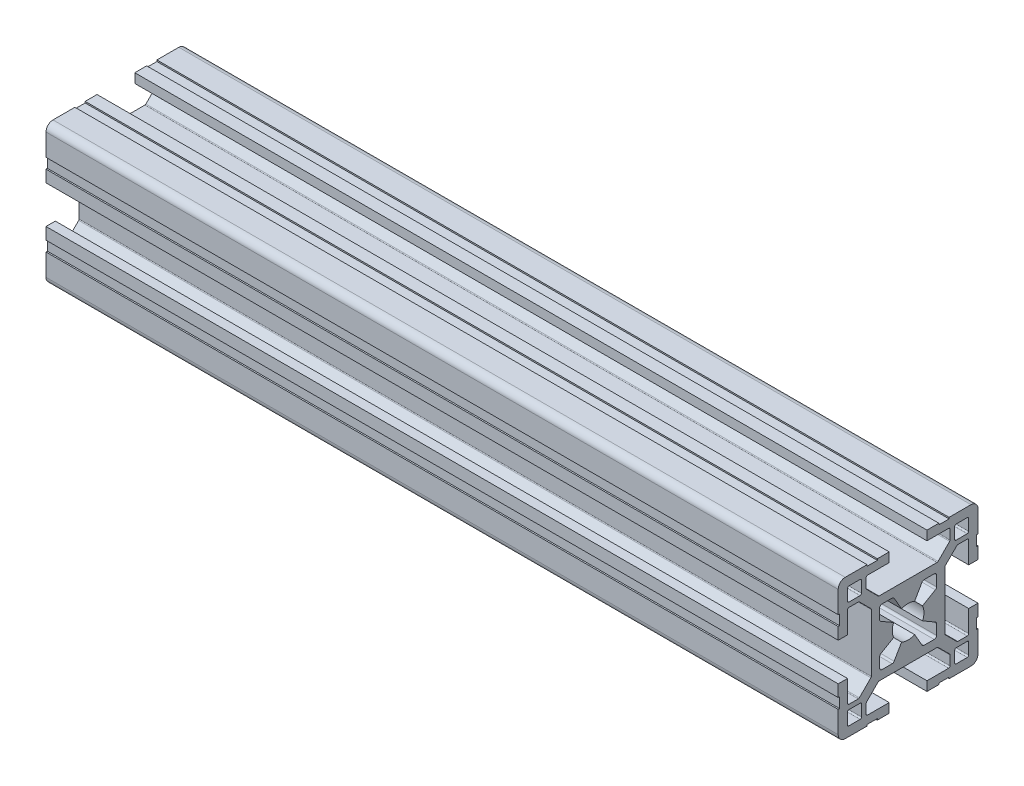
SolidWorks part; units mm, degrees
material "6063-T5"
ref_plane "Plano frontal" through (0, 0, 0) normal (0, 0, 1) x (1, 0, 0)
ref_plane "Plano superior" through (0, 0, 0) normal (0, 1, 0) x (1, 0, 0)
ref_plane "Plano direito" through (0, 0, 0) normal (1, 0, 0) x (0, 0, -1)
sketch "Esboço1" plane through (0, 0, 0) normal (0, 0, 1) x (1, 0, 0)
  line L0 (0, 0) -> (170, 0)
  point P3 (85, 0)
  dimension "D1" = 170
other "Quadrado PF30-11 - PERFIL 3030 CENTRO M8(1)"
ref_plane "Plano1" through (0, 0, 0) normal (1, 0, 0) x (0, 1, 0)
sketch "Sketch1" plane through (0, 0, 0) normal (1, 0, 0) x (0, 1, 0)
  line L0 (-6.1, -3.4254) -> (-6.1, -5.6)
  line L1 (-5.6, -6.1) -> (-3.4254, -6.1)
  line L2 (3.4254, -6.1) -> (5.6, -6.1)
  line L3 (6.1, -5.6) -> (6.1, -3.4254)
  line L4 (6.1, 3.4254) -> (6.1, 5.6)
  line L5 (5.6, 6.1) -> (3.4254, 6.1)
  line L6 (-3.4254, 6.1) -> (-5.6, 6.1)
  line L7 (-6.1, 5.6) -> (-6.1, 3.4254)
  line L8 (15, 6.6) -> (14.7, 6.6)
  line L9 (5.85, -2.9924) -> (3.097, -1.403)
  line L10 (10, 12.7) -> (10, 10.3)
  line L11 (13, -12.7) -> (13, -10.3)
  line L12 (-10.3, -10) -> (-12.7, -10)
  line L13 (-13, 12.7) -> (-13, 10.3)
  line L14 (3.097, 1.403) -> (5.85, 2.9924)
  line L15 (2.9924, 5.85) -> (1.403, 3.097)
  line L16 (-1.403, 3.097) -> (-2.9924, 5.85)
  line L17 (-5.85, 2.9924) -> (-3.097, 1.403)
  line L18 (-3.097, -1.403) -> (-5.85, -2.9924)
  line L19 (-2.9924, -5.85) -> (-1.403, -3.097)
  line L20 (1.403, -3.097) -> (2.9924, -5.85)
  line L21 (10.3, 10) -> (12.7, 10)
  line L22 (13, 10.3) -> (13, 12.7)
  line L23 (12.7, 13) -> (10.3, 13)
  line L24 (12.7, -10) -> (10.3, -10)
  line L25 (10, -10.3) -> (10, -12.7)
  line L26 (10.3, -13) -> (12.7, -13)
  line L27 (-13, -10.3) -> (-13, -12.7)
  line L28 (-12.7, -13) -> (-10.3, -13)
  line L29 (-10, -12.7) -> (-10, -10.3)
  line L30 (-12.7, 10) -> (-10.3, 10)
  line L31 (-10, 10.3) -> (-10, 12.7)
  line L32 (-10.3, 13) -> (-12.7, 13)
  line L33 (15, 4.05) -> (15, 6.6)
  line L34 (13, 4.05) -> (15, 4.05)
  line L35 (13, 8.7) -> (13, 4.05)
  line L36 (10.6799, 9) -> (12.7, 9)
  line L37 (7.9879, 6.4322) -> (10.4678, 8.9121)
  line L38 (7.9, -6.2201) -> (7.9, 6.2201)
  line L39 (10.4678, -8.9121) -> (7.9879, -6.4322)
  line L40 (12.7, -9) -> (10.6799, -9)
  line L41 (13, -4.05) -> (13, -8.7)
  line L42 (15, -4.05) -> (13, -4.05)
  line L43 (15, -6.6) -> (15, -4.05)
  line L44 (14.7, -6.6) -> (15, -6.6)
  line L45 (14.7, -8.8) -> (14.7, -6.6)
  line L46 (15, -8.8) -> (14.7, -8.8)
  line L47 (15, -13.5) -> (15, -8.8)
  line L48 (8.8, -15) -> (13.5, -15)
  line L49 (8.8, -14.7) -> (8.8, -15)
  line L50 (6.6, -14.7) -> (8.8, -14.7)
  line L51 (6.6, -15) -> (6.6, -14.7)
  line L52 (4.05, -15) -> (6.6, -15)
  line L53 (4.05, -13) -> (4.05, -15)
  line L54 (8.7, -13) -> (4.05, -13)
  line L55 (9, -10.6799) -> (9, -12.7)
  line L56 (6.4322, -7.9879) -> (8.9121, -10.4678)
  line L57 (-6.2201, -7.9) -> (6.2201, -7.9)
  line L58 (-8.9121, -10.4678) -> (-6.4322, -7.9879)
  line L59 (-9, -12.7) -> (-9, -10.6799)
  line L60 (-4.05, -13) -> (-8.7, -13)
  line L61 (-4.05, -15) -> (-4.05, -13)
  line L62 (-6.6, -15) -> (-4.05, -15)
  line L63 (-6.6, -14.7) -> (-6.6, -15)
  line L64 (-8.8, -14.7) -> (-6.6, -14.7)
  line L65 (-8.8, -15) -> (-8.8, -14.7)
  line L66 (-13.5, -15) -> (-8.8, -15)
  line L67 (-15, -8.8) -> (-15, -13.5)
  line L68 (-14.7, -8.8) -> (-15, -8.8)
  line L69 (-14.7, -6.6) -> (-14.7, -8.8)
  line L70 (-15, -6.6) -> (-14.7, -6.6)
  line L71 (-15, -4.05) -> (-15, -6.6)
  line L72 (-13, -4.05) -> (-15, -4.05)
  line L73 (-13, -8.7) -> (-13, -4.05)
  line L74 (-10.6799, -9) -> (-12.7, -9)
  line L75 (-7.9879, -6.4322) -> (-10.4678, -8.9121)
  line L76 (-7.9, 6.2201) -> (-7.9, -6.2201)
  line L77 (-10.4678, 8.9121) -> (-7.9879, 6.4322)
  line L78 (-12.7, 9) -> (-10.6799, 9)
  line L79 (-13, 4.05) -> (-13, 8.7)
  line L80 (-15, 4.05) -> (-13, 4.05)
  line L81 (-15, 6.6) -> (-15, 4.05)
  line L82 (-14.7, 6.6) -> (-15, 6.6)
  line L83 (-14.7, 8.8) -> (-14.7, 6.6)
  line L84 (-15, 8.8) -> (-14.7, 8.8)
  line L85 (-15, 13.5) -> (-15, 8.8)
  line L86 (-8.8, 15) -> (-13.5, 15)
  line L87 (-8.8, 14.7) -> (-8.8, 15)
  line L88 (-6.6, 14.7) -> (-8.8, 14.7)
  line L89 (-6.6, 15) -> (-6.6, 14.7)
  line L90 (-4.05, 15) -> (-6.6, 15)
  line L91 (-4.05, 13) -> (-4.05, 15)
  line L92 (-8.7, 13) -> (-4.05, 13)
  line L93 (-9, 10.6799) -> (-9, 12.7)
  line L94 (-6.4322, 7.9879) -> (-8.9121, 10.4678)
  line L95 (6.2201, 7.9) -> (-6.2201, 7.9)
  line L96 (8.9121, 10.4678) -> (6.4322, 7.9879)
  line L97 (9, 12.7) -> (9, 10.6799)
  line L98 (4.05, 13) -> (8.7, 13)
  line L99 (4.05, 15) -> (4.05, 13)
  line L100 (6.6, 15) -> (4.05, 15)
  line L101 (6.6, 14.7) -> (6.6, 15)
  line L102 (8.8, 14.7) -> (6.6, 14.7)
  line L103 (8.8, 15) -> (8.8, 14.7)
  line L104 (13.5, 15) -> (8.8, 15)
  line L105 (15, 8.8) -> (15, 13.5)
  line L106 (14.7, 8.8) -> (15, 8.8)
  line L107 (14.7, 6.6) -> (14.7, 8.8)
  arc A0 (-5.85, -2.9924) -> (-6.1, -3.4254) centre (-5.6, -3.4254) ccw
  arc A1 (-6.1, -5.6) -> (-5.6, -6.1) centre (-5.6, -5.6) ccw
  arc A2 (-3.4254, -6.1) -> (-2.9924, -5.85) centre (-3.4254, -5.6) ccw
  arc A3 (2.9924, -5.85) -> (3.4254, -6.1) centre (3.4254, -5.6) ccw
  arc A4 (5.6, -6.1) -> (6.1, -5.6) centre (5.6, -5.6) ccw
  arc A5 (6.1, -3.4254) -> (5.85, -2.9924) centre (5.6, -3.4254) ccw
  arc A6 (5.85, 2.9924) -> (6.1, 3.4254) centre (5.6, 3.4254) ccw
  arc A7 (6.1, 5.6) -> (5.6, 6.1) centre (5.6, 5.6) ccw
  arc A8 (3.4254, 6.1) -> (2.9924, 5.85) centre (3.4254, 5.6) ccw
  arc A9 (-2.9924, 5.85) -> (-3.4254, 6.1) centre (-3.4254, 5.6) ccw
  arc A10 (-5.6, 6.1) -> (-6.1, 5.6) centre (-5.6, 5.6) ccw
  arc A11 (-6.1, 3.4254) -> (-5.85, 2.9924) centre (-5.6, 3.4254) ccw
  arc A12 (3.097, -1.403) -> (3.097, 1.403) centre (0, 0) ccw
  arc A13 (1.403, 3.097) -> (-1.403, 3.097) centre (0, 0) ccw
  arc A14 (-3.097, 1.403) -> (-3.097, -1.403) centre (0, 0) ccw
  arc A15 (-1.403, -3.097) -> (1.403, -3.097) centre (0, 0) ccw
  arc A16 (10, 10.3) -> (10.3, 10) centre (10.3, 10.3) ccw
  arc A17 (12.7, 10) -> (13, 10.3) centre (12.7, 10.3) ccw
  arc A18 (13, 12.7) -> (12.7, 13) centre (12.7, 12.7) ccw
  arc A19 (10.3, 13) -> (10, 12.7) centre (10.3, 12.7) ccw
  arc A20 (13, -10.3) -> (12.7, -10) centre (12.7, -10.3) ccw
  arc A21 (10.3, -10) -> (10, -10.3) centre (10.3, -10.3) ccw
  arc A22 (10, -12.7) -> (10.3, -13) centre (10.3, -12.7) ccw
  arc A23 (12.7, -13) -> (13, -12.7) centre (12.7, -12.7) ccw
  arc A24 (-12.7, -10) -> (-13, -10.3) centre (-12.7, -10.3) ccw
  arc A25 (-13, -12.7) -> (-12.7, -13) centre (-12.7, -12.7) ccw
  arc A26 (-10.3, -13) -> (-10, -12.7) centre (-10.3, -12.7) ccw
  arc A27 (-10, -10.3) -> (-10.3, -10) centre (-10.3, -10.3) ccw
  arc A28 (-13, 10.3) -> (-12.7, 10) centre (-12.7, 10.3) ccw
  arc A29 (-10.3, 10) -> (-10, 10.3) centre (-10.3, 10.3) ccw
  arc A30 (-10, 12.7) -> (-10.3, 13) centre (-10.3, 12.7) ccw
  arc A31 (-12.7, 13) -> (-13, 12.7) centre (-12.7, 12.7) ccw
  arc A32 (13, 8.7) -> (12.7, 9) centre (12.7, 8.7) ccw
  arc A33 (10.6799, 9) -> (10.4678, 8.9121) centre (10.6799, 8.7) ccw
  arc A34 (7.9879, 6.4322) -> (7.9, 6.2201) centre (8.2, 6.2201) ccw
  arc A35 (7.9, -6.2201) -> (7.9879, -6.4322) centre (8.2, -6.2201) ccw
  arc A36 (10.4678, -8.9121) -> (10.6799, -9) centre (10.6799, -8.7) ccw
  arc A37 (12.7, -9) -> (13, -8.7) centre (12.7, -8.7) ccw
  arc A38 (13.5, -15) -> (15, -13.5) centre (13.5, -13.5) ccw
  arc A39 (8.7, -13) -> (9, -12.7) centre (8.7, -12.7) ccw
  arc A40 (9, -10.6799) -> (8.9121, -10.4678) centre (8.7, -10.6799) ccw
  arc A41 (6.4322, -7.9879) -> (6.2201, -7.9) centre (6.2201, -8.2) ccw
  arc A42 (-6.2201, -7.9) -> (-6.4322, -7.9879) centre (-6.2201, -8.2) ccw
  arc A43 (-8.9121, -10.4678) -> (-9, -10.6799) centre (-8.7, -10.6799) ccw
  arc A44 (-9, -12.7) -> (-8.7, -13) centre (-8.7, -12.7) ccw
  arc A45 (-15, -13.5) -> (-13.5, -15) centre (-13.5, -13.5) ccw
  arc A46 (-13, -8.7) -> (-12.7, -9) centre (-12.7, -8.7) ccw
  arc A47 (-10.6799, -9) -> (-10.4678, -8.9121) centre (-10.6799, -8.7) ccw
  arc A48 (-7.9879, -6.4322) -> (-7.9, -6.2201) centre (-8.2, -6.2201) ccw
  arc A49 (-7.9, 6.2201) -> (-7.9879, 6.4322) centre (-8.2, 6.2201) ccw
  arc A50 (-10.4678, 8.9121) -> (-10.6799, 9) centre (-10.6799, 8.7) ccw
  arc A51 (-12.7, 9) -> (-13, 8.7) centre (-12.7, 8.7) ccw
  arc A52 (-13.5, 15) -> (-15, 13.5) centre (-13.5, 13.5) ccw
  arc A53 (-8.7, 13) -> (-9, 12.7) centre (-8.7, 12.7) ccw
  arc A54 (-9, 10.6799) -> (-8.9121, 10.4678) centre (-8.7, 10.6799) ccw
  arc A55 (-6.4322, 7.9879) -> (-6.2201, 7.9) centre (-6.2201, 8.2) ccw
  arc A56 (6.2201, 7.9) -> (6.4322, 7.9879) centre (6.2201, 8.2) ccw
  arc A57 (8.9121, 10.4678) -> (9, 10.6799) centre (8.7, 10.6799) ccw
  arc A58 (9, 12.7) -> (8.7, 13) centre (8.7, 12.7) ccw
  arc A59 (15, 13.5) -> (13.5, 15) centre (13.5, 13.5) ccw
  point P1 (0, 0)
  point P2 (0, 0)
  point P3 (-15, -15)
  point P4 (0, -15)
  point P5 (-15, 0)
  point P230 (-15, 15)
  point P231 (0, 15)
  point P232 (15, 15)
  point P233 (15, 0)
  point P234 (15, -15)
  point P235 (0, -15)
  point P236 (-15, -15)
  point P237 (-15, 0)
  point P238 (0, 0)
  point P239 (0, 0)
